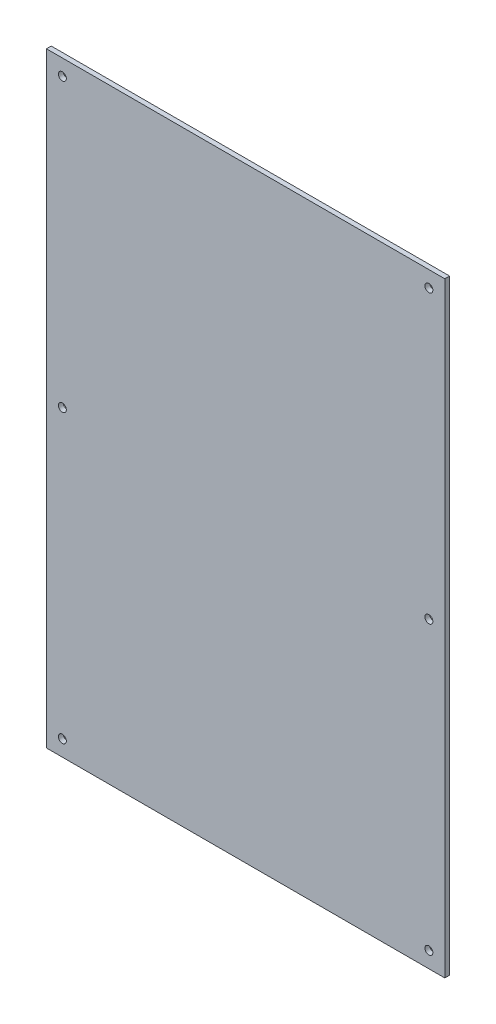
SolidWorks part; units mm, degrees
ref_plane "Plan de face" through (0, 0, 0) normal (0, 0, 1) x (1, 0, 0)
ref_plane "Plan de dessus" through (0, 0, 0) normal (0, 1, 0) x (1, 0, 0)
ref_plane "Plan de droite" through (0, 0, 0) normal (1, 0, 0) x (0, 0, -1)
sketch "Esquisse1" plane through (0, 0, 0) normal (0, 0, 1) x (1, 0, 0)
  line L1 (87.3378, 66.1472) -> (-35.1622, 66.1472)
  line L2 (214.8378, 66.1472) -> (214.8378, -313.8528)
  line L3 (87.3378, -313.8528) -> (-35.1622, -313.8528)
  line L4 (-35.1622, 66.1472) -> (-35.1622, -313.8528)
  line L6 (92.3378, -313.8528) -> (214.8378, -313.8528)
  line L7 (87.3378, -313.8528) -> (92.3378, -313.8528)
  line L9 (92.3378, 66.1472) -> (214.8378, 66.1472)
  line L10 (-35.1622, -123.8528) -> (214.8378, -123.8528) construction
  line L11 (87.3378, 66.1472) -> (92.3378, 66.1472)
  line L20 (89.8378, 63.6472) -> (89.8378, -311.3528) construction
  line L22 (93.8378, 46.1472) -> (93.8378, 49.6472) construction
  circle A10 centre (-25.1622, 56.1472) radius 2.5
  circle A11 centre (204.8378, 56.1472) radius 2.5
  circle A12 centre (204.8378, -303.8528) radius 2.5
  circle A13 centre (-25.1622, -303.8528) radius 2.5
  circle A14 centre (204.8378, -123.8528) radius 2.5
  circle A15 centre (-25.1622, -123.8528) radius 2.5
  dimension "D6" = 190
  dimension "D40" = 5
  dimension "D1" = 250
  dimension "D2" = 190
  dimension "D4" = 190
  dimension "D5" = 190
  dimension "D36" = 122.5
  dimension "D38" = 10
  dimension "D39" = 10
  dimension "D41" = 10
extrude "Boss.-Extru.1" add sketch "Esquisse1" along normal blind 3
